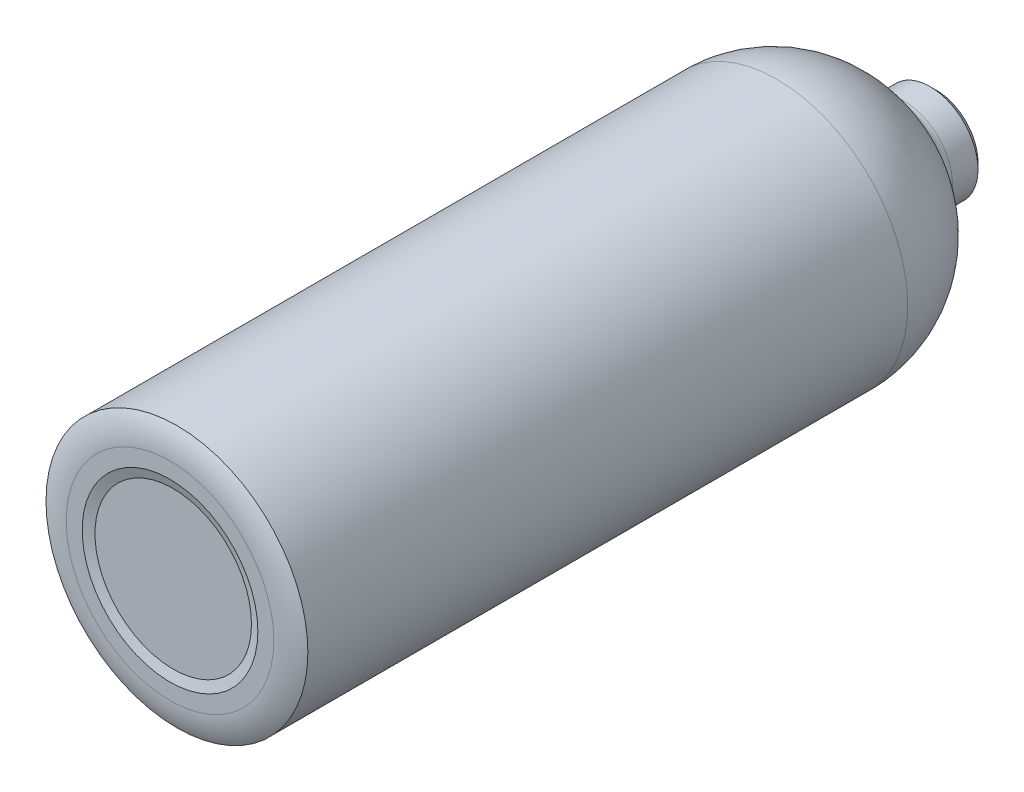
SolidWorks part; units mm, degrees
material "1060 Alloy"
ref_plane "Front Plane" through (0, 0, 0) normal (0, 0, 1) x (1, 0, 0)
ref_plane "Top Plane" through (0, 0, 0) normal (0, 1, 0) x (1, 0, 0)
ref_plane "Right Plane" through (0, 0, 0) normal (1, 0, 0) x (0, 0, -1)
sketch "Sketch1" plane through (0, 0, 0) normal (0, 1, 0) x (1, 0, 0)
  line L0 (-34, -46.1638) -> (0, -46.1638)
  line L1 (0, -52.2686) -> (-24.5, -52.2686)
  line L2 (-24.5, -52.2686) -> (-27.5, -53.2686)
  line L3 (-27.5, -53.2686) -> (-32.5, -53.2686)
  line L4 (-41, -51.1062) -> (-41, 136.7314)
  line L5 (-8, 186.7314) -> (-13, 186.7314)
  line L6 (-13, 186.7314) -> (-15, 184.7314)
  line L7 (-15, 184.7314) -> (-15, 176.7314)
  line L8 (0, -52.2686) -> (0, -46.1638)
  line L11 (-8, 179.7314) -> (-8, 179.7314)
  line L12 (-8, 179.7314) -> (-8, 176.7314)
  line L13 (-34, -46.1638) -> (-34, 136.7314)
  line L17 (-8, 179.7314) -> (-8, 186.7314)
  line L19 (-7, -45.2686) -> (-7, 179.7314) construction
  line L20 (0, -46.1638) -> (0, -83.5493) construction
  line L21 (0, -52.2686) -> (0, 186.7314) construction
  line L22 (0, 186.7314) -> (-13, 186.7314) construction
  line L23 (-7, 179.7314) -> (-8, 179.7314) construction
  line L24 (-7, -45.2686) -> (-25.6359, -45.2686) construction
  line L25 (-25.6359, -45.2686) -> (-28.6359, -46.2686) construction
  line L26 (-28.6359, -46.2686) -> (-32.5, -46.2686) construction
  arc A0 (-32.5, -53.2686) -> (-41, -51.1062) centre (-32.5, -35.4814) cw
  arc A1 (-15, 176.7314) -> (-18.25, 171.7314) centre (-20.4712, 176.7314) cw
  arc A2 (-41, 136.7314) -> (-18.25, 171.7314) centre (-2.7019, 136.7314) cw
  arc A3 (-8, 176.7314) -> (-15.4082, 165.3342) centre (-20.4712, 176.7314) cw
  arc A4 (-34, 136.7314) -> (-15.4082, 165.3342) centre (-2.7019, 136.7314) cw
  arc A6 (-32.5, -46.2686) -> (-34, -46.1638) centre (-32.5, -35.4814) cw construction
  dimension "D1" = 24.5
  dimension "D2" = 1
  dimension "D3" = 3
  dimension "D6" = 190
  dimension "D7" = 240
  dimension "D9" = 2
  dimension "D10" = 2
  dimension "D11" = 10
  dimension "D12" = 225
  dimension "D13" = 7
revolve "Revolve1" add sketch "Sketch1" angle 360 about L8
